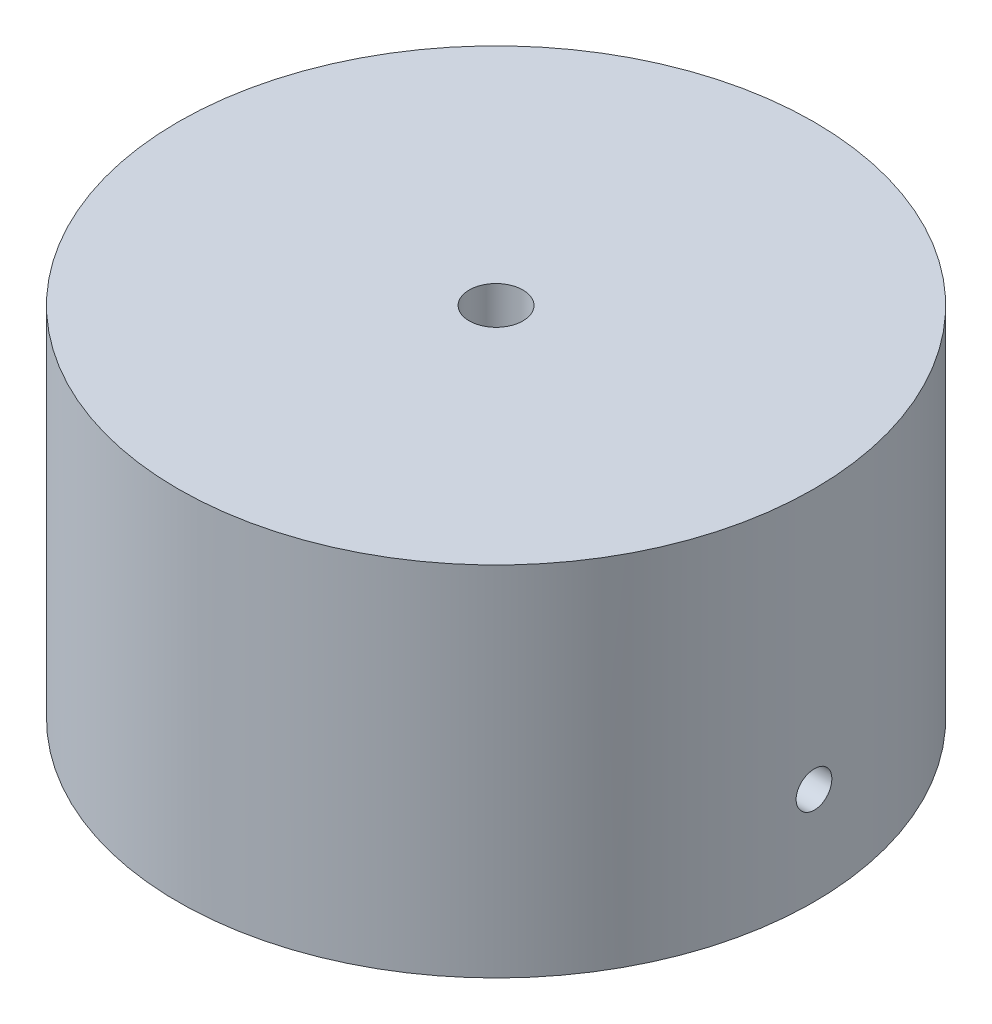
SolidWorks part; units mm, degrees
ref_plane "Plan de face" through (0, 0, 0) normal (0, 0, 1) x (1, 0, 0)
ref_plane "Plan de dessus" through (0, 0, 0) normal (0, 1, 0) x (1, 0, 0)
ref_plane "Plan de droite" through (0, 0, 0) normal (1, 0, 0) x (0, 0, -1)
sketch "Esquisse1" plane through (0, 0, 0) normal (0, 1, 0) x (1, 0, 0)
  circle A0 centre (0, 0) radius 40
  dimension "D1" = 80
extrude "Boss.-Extru.1" add sketch "Esquisse1" along normal blind 15
sketch "Esquisse5" plane through (0, 0, 0) normal (0, -1, 0) x (1, 0, 0)
  circle A0 centre (0, 0) radius 35.1
  circle A1 centre (0, 0) radius 40
extrude "Boss.-Extru.2" add sketch "Esquisse5" along normal blind 30
hole_wizard "Dégagement M41" positions "Esquisse3D2" profile "Esquisse6" hole size "M4" standard "ISO"
sketch3d "Esquisse3D2"
  point P0 (40, -17.7608, -0.0618)
sketch "Esquisse6" plane through (40, -17.7608, -0.0618) normal (0, 1, 0) x (-0.0015, 0, -1)
  line L0 (0, 0) -> (0, 4.9)
  line L1 (0, 4.9) -> (2.25, 4.9)
  line L2 (2.25, 4.9) -> (2.25, 0)
  line L5 (2.25, 0) -> (0, 0)
  line L11 (0, -6.35) -> (0, 107.95) construction
  dimension "Diamètre du perçage jusqu'au prochain" = 4.5
  dimension "Profondeur du perçage jusqu'au prochain" = 4.9
sketch "Esquisse10" plane through (0, 15, 0) normal (0, 1, 0) x (1, 0, 0)
  point P0 (0, 0)
  point P1 (0, 0)
hole_wizard "Dégagement 1/41" positions "Esquisse3D7" profile "Esquisse11" hole size "1/4" standard "Ansi Inch"
sketch3d "Esquisse3D7"
  point P0 (0, 0, 0)
  point P3 (0, 15, 0)
  point P6 (0.1084, 15, 0.0819)
sketch "Esquisse11" plane through (0, 15, 0) normal (1, 0, 0) x (0, 0, 1)
  line L0 (0, 0) -> (0, 12.0298)
  line L1 (0, 12.0298) -> (3.3782, 10)
  line L2 (3.3782, 10) -> (3.3782, 0)
  line L5 (3.3782, 0) -> (0, 0)
  line L10 (0, 12.0298) -> (-3.3782, 10) construction
  line L11 (0, -6.35) -> (0, 107.95) construction
  dimension "Diamètre du perçage" = 6.7564
  dimension "Profondeur du perçage" = 10
  dimension "Angle de pointe" = 118
